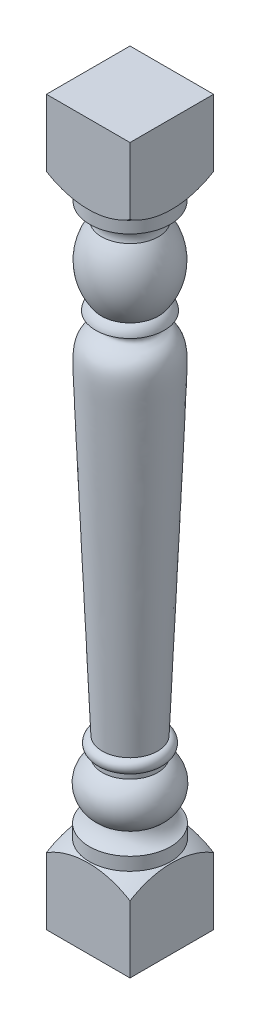
SolidWorks part; units mm, degrees
ref_plane "Front Plane" through (0, 0, 0) normal (0, 0, 1) x (1, 0, 0)
ref_plane "Top Plane" through (0, 0, 0) normal (0, 1, 0) x (1, 0, 0)
ref_plane "Right Plane" through (0, 0, 0) normal (1, 0, 0) x (0, 0, -1)
sketch "Sketch1" plane through (0, 0, 0) normal (0, 0, 1) x (1, 0, 0)
  line L0 (0, 0) -> (0, 965.2) construction
  line L1 (0, -614.68) -> (0, 614.68) construction
  line L2 (0, 965.2) -> (2.54, 965.2) construction
  line L3 (2.54, 965.2) -> (2.54, 942.975) construction
  line L4 (24.13, 130.175) -> (24.13, 120.65) construction
  line L6 (1.905, 0) -> (1.905, 22.225) construction
  arc A0 (2.54, 942.975) -> (22.86, 914.4) centre (-6.6011, 914.9623) cw construction
  arc A1 (22.86, 796.925) -> (22.86, 914.4) centre (97.594, 855.6625) cw construction
  arc A2 (22.86, 796.925) -> (12.7, 781.05) centre (35.8871, 777.399) ccw construction
  arc A3 (24.13, 152.4) -> (24.13, 130.175) centre (25.1271, 141.2875) ccw construction
  arc A4 (1.905, 22.225) -> (22.86, 44.45) centre (-4.0093, 48.7927) ccw construction
  arc A5 (24.13, 120.65) -> (22.86, 44.45) centre (45.3767, 82.1853) ccw construction
  spline S0 degree 3 poles (12.7, 781.05) (20.4619, 780.6915) (49.8326, 761.459) (-1.3952, 733.4357) (9.6428, 585.614) (9.4613, 519.9517) (24.13, 152.4) knots 0 0 0 0 0.151522 0.286773 0.373312 1 1 1 1 construction
  point P5 (2.54, 965.2)
  point P6 (2.54, 942.975)
  point P7 (22.86, 914.4)
  point P12 (2.54, 855.6625)
  point P13 (22.86, 796.925)
  point P14 (12.7, 781.05)
  point P19 (2.54, 714.375)
  point P20 (24.13, 152.4)
  point P22 (24.13, 130.175)
  point P24 (13.97, 141.2875)
  point P28 (24.13, 120.65)
  point P29 (1.524, 79.375)
  point P31 (22.86, 44.45)
  point P32 (1.905, 22.225)
  point P34 (1.905, 0)
  dimension "D1" = 965.2
sketch "Sketch2" plane through (0, 0, 0) normal (0, 0, 1) x (1, 0, 0)
  line L0 (0, -135.6134) -> (0, 0) construction
  line L1 (0, -642.62) -> (0, 642.62) construction
  line L2 (0, -135.6134) -> (71.4375, -135.6134)
  line L3 (71.4375, -135.6134) -> (71.4375, 1101.1371)
  line L4 (71.4375, 1101.1371) -> (0, 1101.1371)
  line L5 (0, 1101.1371) -> (0, 965.2) construction
  line L6 (-80.9625, 1101.1371) -> (0, 1101.1371)
  line L7 (2.54, 965.2) -> (2.54, 942.975)
  line L8 (0, -135.6134) -> (-80.9625, -135.6134)
  line L9 (1.905, 0) -> (1.905, 22.225)
  line L10 (24.13, 120.65) -> (24.13, 130.175)
  arc A0 (1.905, 22.225) -> (22.86, 44.45) centre (-12.3934, 56.6976) ccw
  arc A1 (24.13, 120.65) -> (22.86, 44.45) centre (45.3767, 82.1853) ccw
  arc A2 (24.13, 152.4) -> (24.13, 130.175) centre (25.1271, 141.2875) ccw
  arc A3 (2.54, 942.975) -> (22.86, 914.4) centre (1.9595, 921.0498) cw
  arc A4 (22.86, 914.4) -> (2.54, 942.975) centre (-6.6011, 914.9623) ccw construction
  arc A5 (22.86, 914.4) -> (22.86, 796.925) centre (97.594, 855.6625) ccw
  arc A6 (22.86, 796.925) -> (12.7, 781.05) centre (35.8871, 777.399) ccw
  arc A7 (1.905, 0) -> (-80.9625, -135.6134) centre (71.4375, -135.6134) ccw
  arc A8 (2.54, 965.2) -> (-80.9625, 1101.1371) centre (71.4375, 1101.1371) cw
  spline S0 degree 3 poles (12.7, 781.05) (28.5433, 778.2125) (43.2563, 750.6902) (-0.0352, 758.0128) (6.5863, 584.7537) (4.6831, 626.5173) (24.13, 152.4) knots 0 0 0 0 0.117084 0.342939 0.431231 1 1 1 1
  dimension "D1" = 152.4
  dimension "D3" = 152.4
  dimension "D2" = 71.4375
revolve "Revolve2" add sketch "Sketch2" angle 360 about L3
sketch "Sketch4" plane through (0, 0, 0) normal (0, 1, 0) x (1, 0, 0)
  line L1 (0, 71.4375) -> (142.875, 71.4375)
  line L2 (0, 71.4375) -> (0, -71.4375)
  line L3 (0, -71.4375) -> (142.875, -71.4375)
  line L4 (142.875, 71.4375) -> (142.875, -71.4375)
  point P4 (0, 0)
  dimension "D1" = 142.875
extrude "Cut-Extrude2" cut sketch "Sketch4" against normal through all and the other way through all flip side to cut
